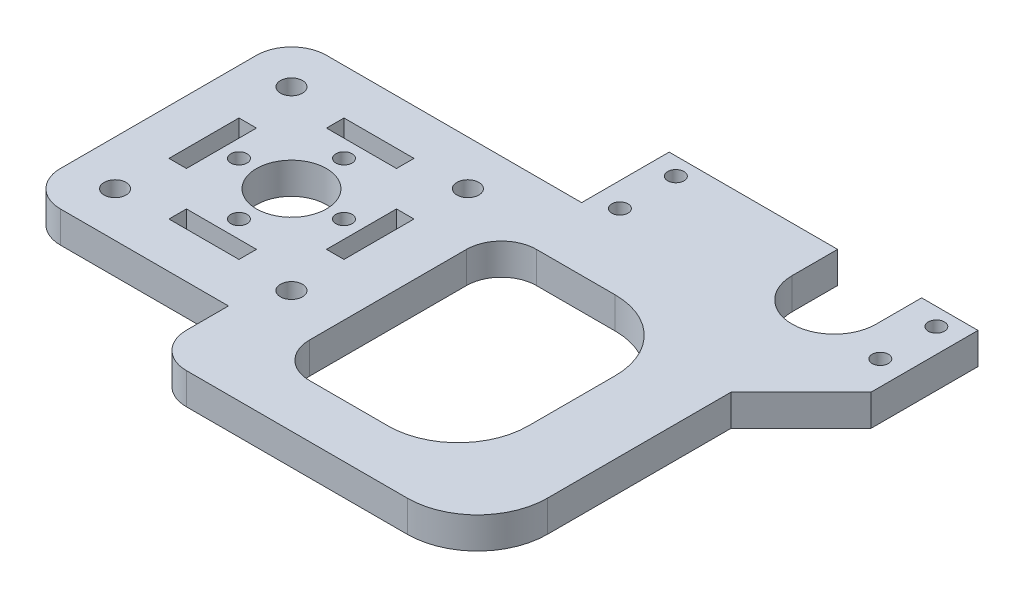
SolidWorks part; units mm, degrees
ref_plane "Front Plane" through (0, 0, 0) normal (0, 0, 1) x (1, 0, 0)
ref_plane "Top Plane" through (0, 0, 0) normal (0, 1, 0) x (1, 0, 0)
ref_plane "Right Plane" through (0, 0, 0) normal (1, 0, 0) x (0, 0, -1)
sketch "Sketch1" plane through (0, 0, 0) normal (0, 1, 0) x (1, 0, 0)
  line L0 (28.4988, 40.005) -> (28.4988, 24.13)
  line L1 (32.893, 26.67) -> (80.137, 26.67) construction
  line L2 (32.893, 26.67) -> (32.893, 36.83) construction
  line L3 (32.893, 36.83) -> (80.137, 36.83) construction
  line L4 (80.137, 26.67) -> (80.137, 36.83) construction
  line L5 (32.893, 26.67) -> (80.137, 36.83) construction
  line L6 (32.893, 36.83) -> (80.137, 26.67) construction
  line L7 (28.4988, 24.13) -> (0, 24.13)
  line L8 (28.4988, 40.005) -> (59.055, 40.005)
  line L9 (84.5185, 40.005) -> (84.5185, 20.6375)
  line L10 (58.7375, 12.6873) -> (25.4, 12.6873)
  line L11 (133.3679, 11.0998) -> (-65.8855, 11.0998) construction
  line L12 (57.15, 11.0998) -> (57.15, -31.3489) construction
  line L13 (58.7375, 12.6873) -> (58.7375, -28.4988)
  line L14 (-5.2962, 0) -> (42.3741, 0) construction
  line L15 (133.3679, -11.0998) -> (-65.8855, -11.0998) construction
  line L16 (25.4, -28.4988) -> (58.7375, -28.4988)
  line L17 (21.7805, 47.4837) -> (21.7805, -50.1661) construction
  line L18 (12.7, -38.1) -> (12.7, -24.13)
  line L19 (-40.2301, -21.7805) -> (138.7399, -21.7805) construction
  line L20 (-17.7759, -26.9113) -> (109.7649, -26.9113) construction
  line L21 (12.7, -24.13) -> (0, -24.13)
  line L22 (12.7, -38.1) -> (71.8185, -38.1)
  line L23 (25.4, -28.4988) -> (25.4, 12.6873)
  line L24 (26.9113, 52.5085) -> (26.9113, -81.7372) construction
  line L25 (11.1125, -56.3839) -> (11.1125, 37.4468) construction
  line L26 (48.7981, 19.05) -> (153.314, 19.05) construction
  line L27 (48.7981, -19.05) -> (147.4153, -19.05) construction
  line L28 (74.295, 40.005) -> (84.5185, 40.005)
  line L29 (-24.13, 0) -> (-24.13, 24.13)
  line L30 (59.055, 31.75) -> (59.055, 40.005)
  line L31 (74.295, 31.75) -> (74.295, 40.005)
  line L32 (84.5185, 20.6375) -> (71.8185, 7.9375)
  line L33 (71.8185, 7.9375) -> (71.8185, -38.1)
  line L34 (-24.13, 24.13) -> (0, 24.13)
  line L35 (-24.13, 0) -> (-24.13, -24.13)
  line L36 (-24.13, -24.13) -> (0, -24.13)
  arc A0 (0, 24.13) -> (0, -24.13) centre (0, 0) ccw construction
  circle A1 centre (32.893, 36.83) radius 2.1844 construction
  circle A2 centre (32.893, 26.67) radius 2.1844 construction
  circle A3 centre (80.137, 26.67) radius 2.1844 construction
  circle A4 centre (80.137, 36.83) radius 2.1844 construction
  arc A5 (59.055, 31.75) -> (74.295, 31.75) centre (66.675, 31.75) ccw
  point P11 (56.515, 31.75)
  dimension "D1" = 48.26
  dimension "D2" = 47.244
  dimension "D6" = 4.3688
  dimension "D7" = 15.24
  dimension "D25" = 38.1
  dimension "D3" = 10.16
  dimension "D4" = 1.5875
  dimension "D5" = 31.75
  dimension "D8" = 13.462
  dimension "D9" = 11.0998
  dimension "D10" = 57.15
  dimension "D11" = 66.675
  dimension "D12" = 3.175
  dimension "D13" = 4.3815
  dimension "D14" = 1.5875
  dimension "D15" = 1.5875
  dimension "D16" = 1.5875
  dimension "D17" = 21.7805
  dimension "D18" = 21.7805
  dimension "D19" = 26.9113
  dimension "D20" = 1.5875
  dimension "D21" = 11.1125
  dimension "D22" = 25.4
  dimension "D23" = 26.9113
  dimension "D24" = 38.1
  dimension "D26" = 135
  dimension "D27" = 19.3675
  dimension "D28" = 12.7
extrude "Boss-Extrude1" add sketch "Sketch1" along normal blind 5.6896
fillet "Fillet1" radius 12.7 2 edges at (58.7375, 2.8448, -12.6873) (58.7375, 2.8448, 28.4988)
fillet "Fillet2" radius 6.35 2 edges at (25.4, 2.8448, 28.4988) (25.4, 2.8448, -12.6873)
sketch "Sketch11" plane through (0, 5.6896, 0) normal (0, 1, 0) x (1, 0, 0)
  circle A0 centre (0, 0) radius 6.35
  dimension "D1" = 12.7
extrude "Cut-Extrude3" cut sketch "Sketch11" against normal up to next
sketch "Sketch8" plane through (0, 5.6896, 0) normal (0, 1, 0) x (1, 0, 0)
  line L0 (0, 0) -> (0, 19.5466) construction
  line L1 (-7.9092, 0) -> (7.9159, 0) construction
  line L2 (-6.35, 15.875) -> (6.35, 15.875)
  line L3 (-6.35, 15.875) -> (-6.35, 12.7)
  line L4 (-6.35, 12.7) -> (6.35, 12.7)
  line L5 (6.35, 15.875) -> (6.35, 12.7)
  line L6 (-6.35, 15.875) -> (6.35, 12.7) construction
  line L7 (-6.35, 12.7) -> (6.35, 15.875) construction
  circle A1 centre (0, 0) radius 6.35 construction
  point P0 (0, 14.2875)
  dimension "D1" = 3.175
  dimension "D2" = 25.4
  dimension "D3" = 12.7
extrude "Cut-Extrude2" cut sketch "Sketch8" against normal up to next (5.6896 mm away)
hole_wizard "#4 Clearance Hole3" positions "Sketch12" profile "Sketch13" hole size "#4" standard "ANSI Inch" end condition up to next
sketch "Sketch12" plane through (0, 5.6896, 0) normal (0, 1, 0) x (1, 0, 0)
  line L0 (0, 6.35) -> (0, 23.0367) construction
  circle A2 centre (0, 0) radius 6.35 construction
  point P0 (0, 9.525)
  dimension "D1" = 9.525
sketch "Sketch13" plane through (0, 5.6896, -9.525) normal (1, 0, 0) x (0, 0, 1)
  line L0 (0, 0) -> (0, 5.6906)
  line L1 (0, 5.6906) -> (1.4732, 5.6906)
  line L2 (1.4732, 5.6906) -> (1.4732, 0)
  line L5 (1.4732, 0) -> (0, 0)
  line L11 (0, -6.35) -> (0, 107.95) construction
  dimension "Thru Hole Dia." = 2.9464
  dimension "Thru Hole Depth" = 5.6906
pattern_circular "CirPattern1" count 4 over 360 about axis through (0, 0, 0) along (0, 1, 0) of "Cut-Extrude2", "#4 Clearance Hole3"
fillet "Fillet3" radius 12.7 1 edges at (71.8185, 2.8448, 38.1)
hole_wizard "#4 Clearance Hole4" positions "Sketch15" profile "Sketch14" hole size "#4" standard "ANSI Inch" end condition through all
sketch "Sketch15" plane through (0, 5.6896, 0) normal (0, 1, 0) x (1, 0, 0)
  point P0 (32.893, 36.83)
  point P3 (80.137, 36.83)
  point P6 (80.137, 26.67)
  point P9 (32.893, 26.67)
sketch "Sketch14" plane through (32.893, 5.6896, -36.83) normal (1, 0, 0) x (0, 0, 1)
  line L0 (0, 0) -> (0, 5.6896)
  line L1 (0, 5.6896) -> (1.4732, 5.6896)
  line L2 (1.4732, 5.6896) -> (1.4732, 0)
  line L5 (1.4732, 0) -> (0, 0)
  line L11 (0, -6.35) -> (0, 107.95) construction
  dimension "Thru Hole Dia." = 2.9464
  dimension "Thru Hole Depth" = 5.6896
hole_wizard "Tap Drill for #4 Helicoil1" positions "Sketch17" profile "Sketch16" hole size "#4-40" standard "ANSI Inch" end condition through all
sketch "Sketch17" plane through (0, 5.6896, 0) normal (0, 1, 0) x (1, 0, 0)
  line L1 (-15.9983, -15.9983) -> (15.9983, -15.9983)
  line L2 (-15.9983, -15.9983) -> (-15.9983, 15.9983)
  line L3 (-15.9983, 15.9983) -> (15.9983, 15.9983)
  line L4 (15.9983, -15.9983) -> (15.9983, 15.9983)
  line L5 (-15.9983, -15.9983) -> (15.9983, 15.9983) construction
  line L6 (-15.9983, 15.9983) -> (15.9983, -15.9983) construction
  point P0 (-15.9983, 15.9983)
  point P2 (15.9983, -15.9983)
  point P4 (15.9983, 15.9983)
  point P6 (-15.9983, -15.9983)
  point P9 (0, 0)
  dimension "D1" = 45.25
sketch "Sketch16" plane through (-15.9983, 5.6896, -15.9983) normal (1, 0, 0) x (0, 0, 1)
  line L0 (0, 0) -> (0, 5.6896)
  line L1 (0, 5.6896) -> (1.9939, 5.6896)
  line L2 (1.9939, 5.6896) -> (1.9939, 0)
  line L5 (1.9939, 0) -> (0, 0)
  line L11 (0, -6.35) -> (0, 107.95) construction
  dimension "Thru Hole Dia." = 3.9878
  dimension "Thru Hole Depth" = 5.6896
fillet "Fillet4" radius 6.35 3 edges at (-24.13, 2.8448, 24.13) (-24.13, 2.8448, -24.13) (12.7, 2.8448, 38.1)
